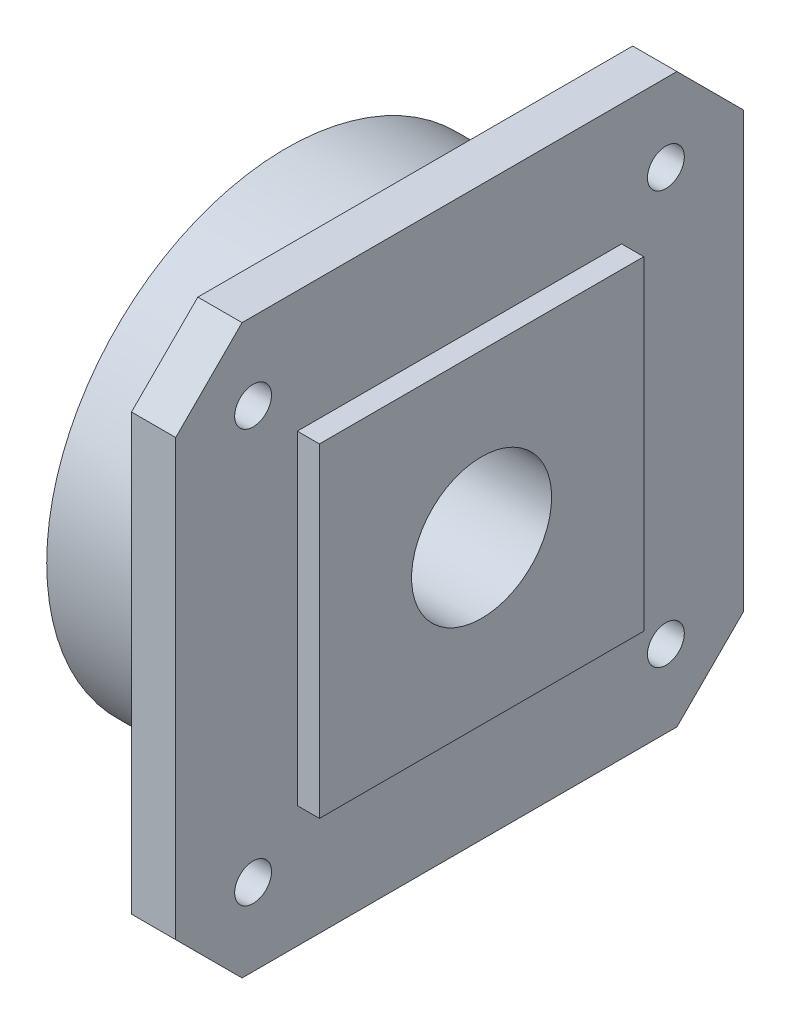
SolidWorks part; units mm, degrees
ref_plane "Front Plane" through (0, 0, 0) normal (0, 0, 1) x (1, 0, 0)
ref_plane "Top Plane" through (0, 0, 0) normal (0, 1, 0) x (1, 0, 0)
ref_plane "Right Plane" through (0, 0, 0) normal (1, 0, 0) x (0, 0, -1)
sketch "Sketch1" plane through (0, 0, 0) normal (1, 0, 0) x (0, 0, -1)
  line L0 (0, 68) -> (9, 77)
  line L1 (9, 0) -> (68, 0)
  line L2 (0, 9) -> (0, 68)
  line L3 (9, 77) -> (68, 77)
  line L4 (77, 9) -> (77, 68)
  line L5 (68, 77) -> (77, 68)
  line L6 (0, 9) -> (9, 0)
  line L7 (68, 0) -> (77, 9)
  dimension "D3" = 59
  dimension "D4" = 59
  dimension "D5" = 59
  dimension "D6" = 59
  dimension "D7" = 9
  dimension "D9" = 9
  dimension "D10" = 9
extrude "Extrude1" add sketch "Sketch1" along normal blind 6
sketch "Sketch2" plane through (6, 0, 0) normal (1, 0, 0) x (0, 0, -1)
  line L0 (0, 68) -> (0, 9) construction
  line L1 (16.5, 60.5) -> (60.5, 60.5)
  line L2 (16.5, 60.5) -> (16.5, 16.5)
  line L3 (16.5, 16.5) -> (60.5, 16.5)
  line L4 (60.5, 60.5) -> (60.5, 16.5)
  line L5 (68, 77) -> (9, 77) construction
  dimension "D1" = 44
  dimension "D2" = 44
  dimension "D3" = 16.5
  dimension "D4" = 16.5
extrude "Extrude2" add sketch "Sketch2" along normal blind 3
sketch "Sketch3" plane through (9, 0, 0) normal (1, 0, 0) x (0, 0, -1)
  line L0 (60.5, 60.5) -> (16.5, 60.5) construction
  line L1 (16.5, 60.5) -> (16.5, 16.5) construction
  circle A0 centre (38.5, 38.5) radius 9.5
  dimension "D3" = 19
  dimension "D1" = 22
  dimension "D2" = 22
sketch "Sketch4" plane through (0, 0, 0) normal (-1, 0, 0) x (0, 0, 1)
  circle A0 centre (-38.5, 38.5) radius 32.5
  dimension "D1" = 65
extrude "Extrude3" add sketch "Sketch4" along normal blind 17.5
extrude "Extrude4" cut sketch "Sketch3" against normal through all
sketch3d "3DSketch1" plane through (0, 0, 0) normal (0, 0, 1) x (1, 0, 0)
  dimension "D1" = 38.5
sketch "Sketch13" plane through (0, 38.5, 0) normal (0, -1, 0) x (1, 0, 0)
  line L0 (9, -38.5) -> (-17.5, -38.5) construction
  line L1 (9, -16.5) -> (9, -60.5) construction
  line L2 (-17.5, -6) -> (-17.5, -71) construction
sketch "Sketch16" plane through (-17.5, 0, 0) normal (-1, 0, 0) x (0, 0, 1)
  line L0 (-17.875, 38.5) -> (17.875, 38.5) construction
  circle A0 centre (-38.5, 38.5) radius 21
  circle A1 centre (-38.5, 38.5) radius 32.5 construction
  dimension "D2" = 42
  dimension "D3" = 0
  dimension "D1" = 0
extrude "Extrude7" cut sketch "Sketch16" against normal blind 12
sketch "Sketch18" plane through (0, 38.5, 0) normal (0, -1, 0) x (1, 0, 0)
  line L0 (-5.5, -56.5) -> (-5.5, -59.5)
  line L1 (-5.5, -17.5) -> (-5.5, -59.5) construction
  line L2 (-5.5, -59.5) -> (-17.5, -59.5)
  line L3 (-17.5, -6) -> (-17.5, -71) construction
  line L4 (-17.5, -59.5) -> (-5.5, -56.5)
  dimension "D1" = 3
revolve "Revolve2" add sketch "Sketch18" angle 360 about L0
sketch "Sketch19" plane through (6, 0, 0) normal (1, 0, 0) x (0, 0, -1)
  line L0 (68, 77) -> (9, 77) construction
  line L1 (0, 68) -> (0, 9) construction
  circle A0 centre (10.5, 66.5) radius 2.5
  dimension "D3" = 5
  dimension "D1" = 10.5
  dimension "D2" = 10.5
extrude "Extrude8" cut sketch "Sketch19" against normal through all
pattern_linear "LPattern1" count 2 spacing 56 along (0, 0, -1) of "Extrude8"
pattern_linear "LPattern2" count 2 spacing 56 along (0, -1, 0) of "LPattern1", "Extrude8"
